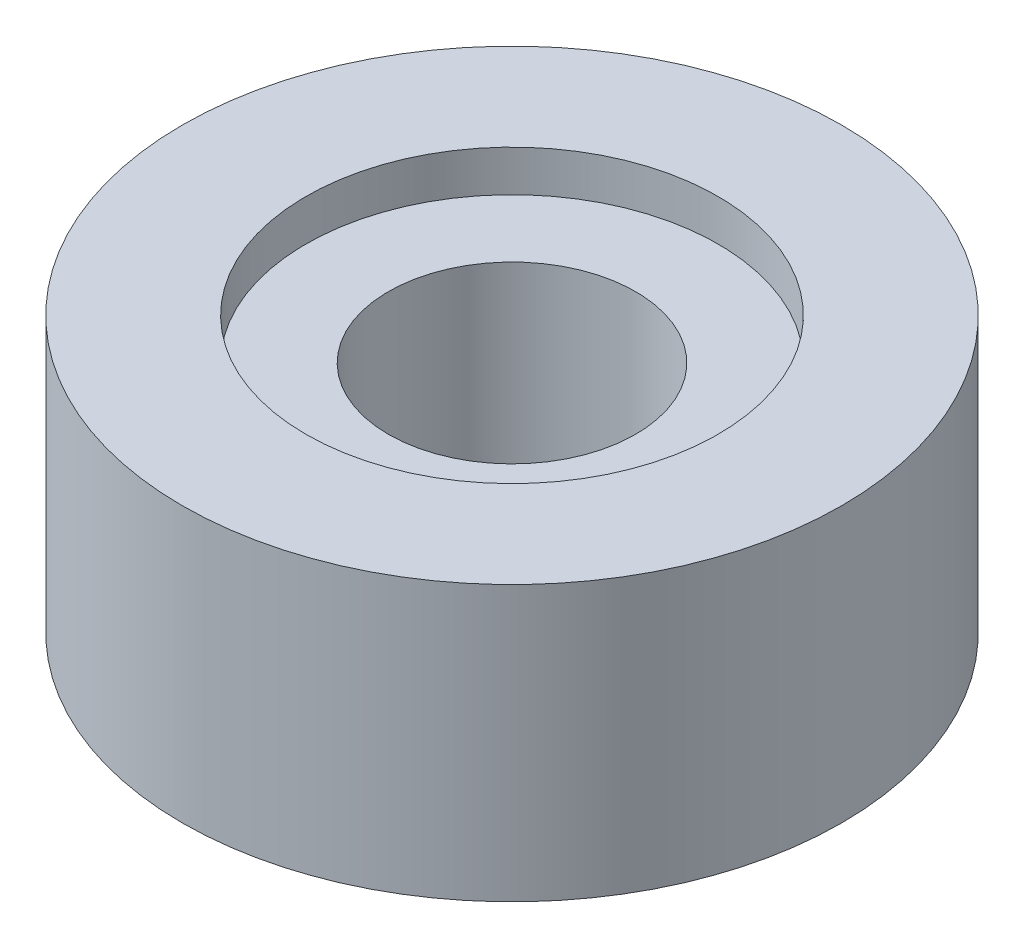
SolidWorks part; units mm, degrees
ref_plane "Plan de face" through (0, 0, 0) normal (0, 0, 1) x (1, 0, 0)
ref_plane "Plan de dessus" through (0, 0, 0) normal (0, 1, 0) x (1, 0, 0)
ref_plane "Plan de droite" through (0, 0, 0) normal (1, 0, 0) x (0, 0, -1)
sketch "Esquisse1" plane through (0, 0, 0) normal (0, 1, 0) x (1, 0, 0)
  circle A0 centre (0, 0) radius 6
  dimension "D1" = 12
extrude "Boss.-Extru.1" add sketch "Esquisse1" along normal blind 5
sketch "Esquisse2" plane through (0, 5, 0) normal (0, 1, 0) x (1, 0, 0)
  circle A0 centre (0, 0) radius 2.25
  dimension "D1" = 4.5
extrude "Enlèv. mat.-Extru.1" cut sketch "Esquisse2" against normal up to next
sketch "Esquisse3" plane through (0, 5, 0) normal (0, 1, 0) x (1, 0, 0)
  circle A0 centre (0, 0) radius 3.75
  dimension "D1" = 7.5
extrude "Enlèv. mat.-Extru.2" cut sketch "Esquisse3" against normal blind 0.75
